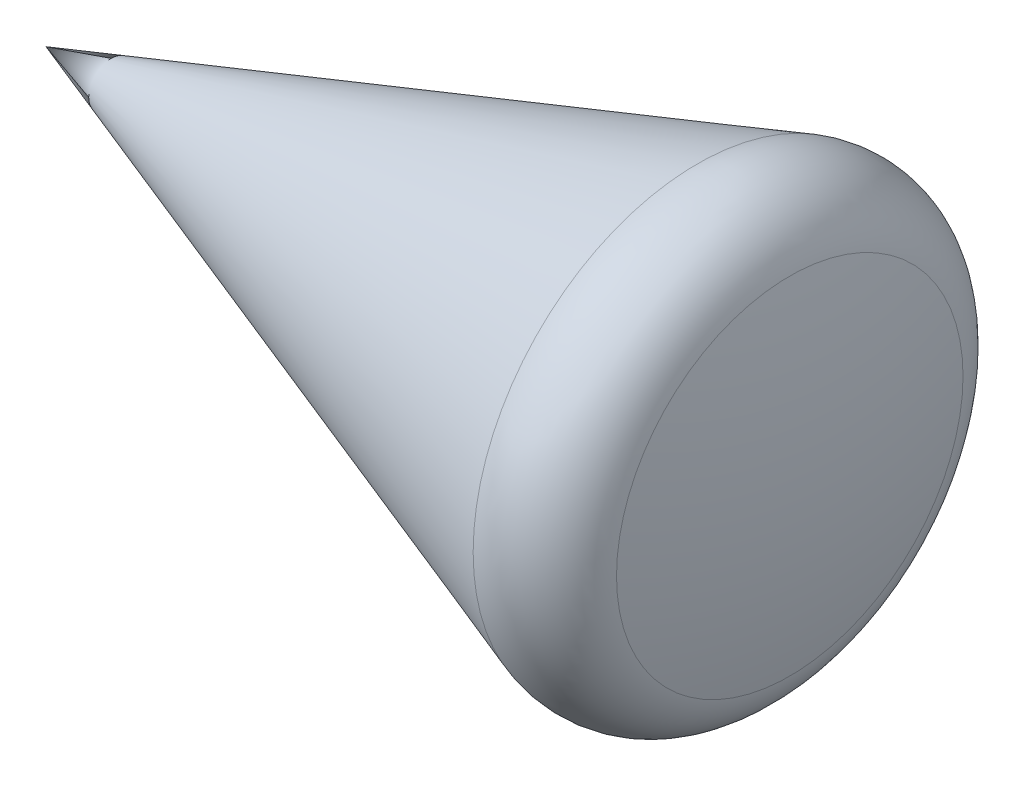
SolidWorks part; units mm, degrees
material "Glass"
ref_plane "Front Plane" through (0, 0, 0) normal (0, 0, 1) x (1, 0, 0)
ref_plane "Top Plane" through (0, 0, 0) normal (0, 1, 0) x (1, 0, 0)
ref_plane "Right Plane" through (0, 0, 0) normal (1, 0, 0) x (0, 0, -1)
sketch "Sketch1" plane through (0, 0, 0) normal (0, 1, 0) x (1, 0, 0)
  line L0 (0, 0) -> (6450, 0)
  line L1 (0, 0) -> (5502.1139, 1894.5297)
  arc A0 (6450, 0) -> (6281.8091, 1463.3436) centre (0, 0) ccw
  arc A1 (5502.1139, 1894.5297) -> (6281.8091, 1463.3436) centre (5697.4548, 1327.2186) cw
  point P3 (6637.2457, 548.4402)
  dimension "D2" = 600
  dimension "D1" = 19
  dimension "D3" = 6450
revolve "Revolve1" add sketch "Sketch1" angle 360 about L0
